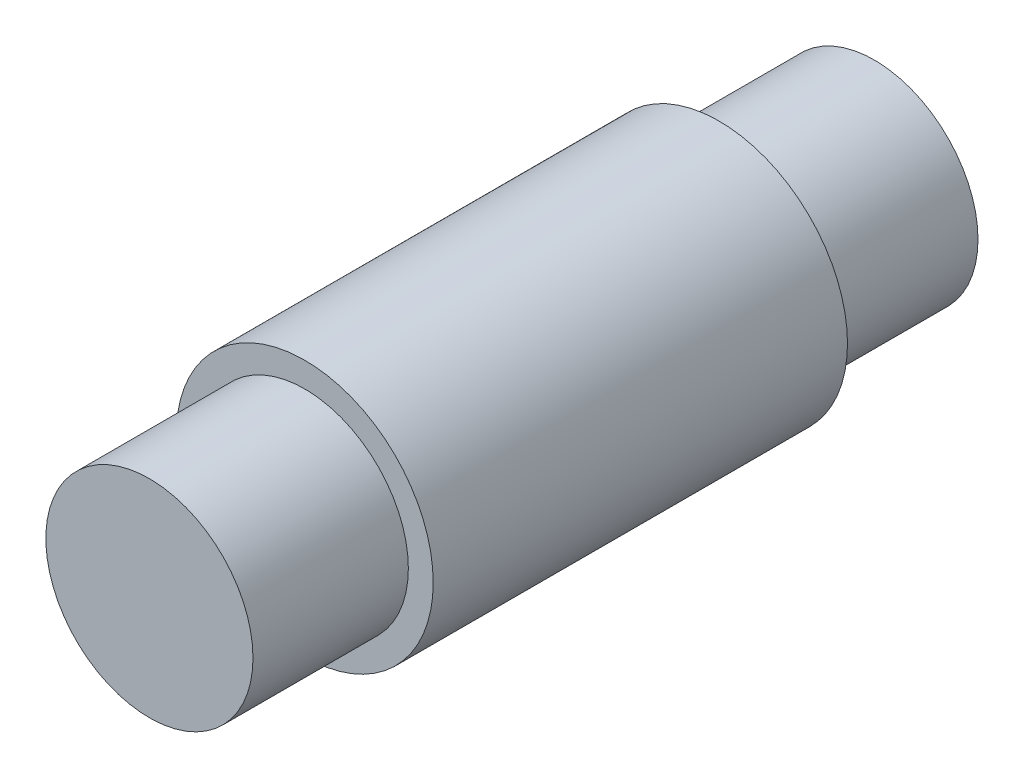
SolidWorks part; units mm, degrees
material "1023 Carbon Steel Sheet (SS)"
ref_plane "Front Plane" through (0, 0, 0) normal (0, 0, 1) x (1, 0, 0)
ref_plane "Top Plane" through (0, 0, 0) normal (0, 1, 0) x (1, 0, 0)
ref_plane "Right Plane" through (0, 0, 0) normal (1, 0, 0) x (0, 0, -1)
sketch "Sketch3" plane through (0, 0, 0) normal (0, 0, 1) x (1, 0, 0)
  circle A0 centre (0, 0) radius 1.55
  dimension "D1" = 3.1
extrude "Boss-Extrude1" add sketch "Sketch3" along normal mid plane 5
sketch "Sketch4" plane through (0, 0, 2.5) normal (0, 0, 1) x (1, 0, 0)
  circle A0 centre (0, 0) radius 1.25
  dimension "D1" = 2.5
extrude "Boss-Extrude2" add sketch "Sketch4" along normal blind 1.875
mirror "Mirror1" about plane through (0, 0, 0) normal (0, 0, 1) of "Boss-Extrude2"
